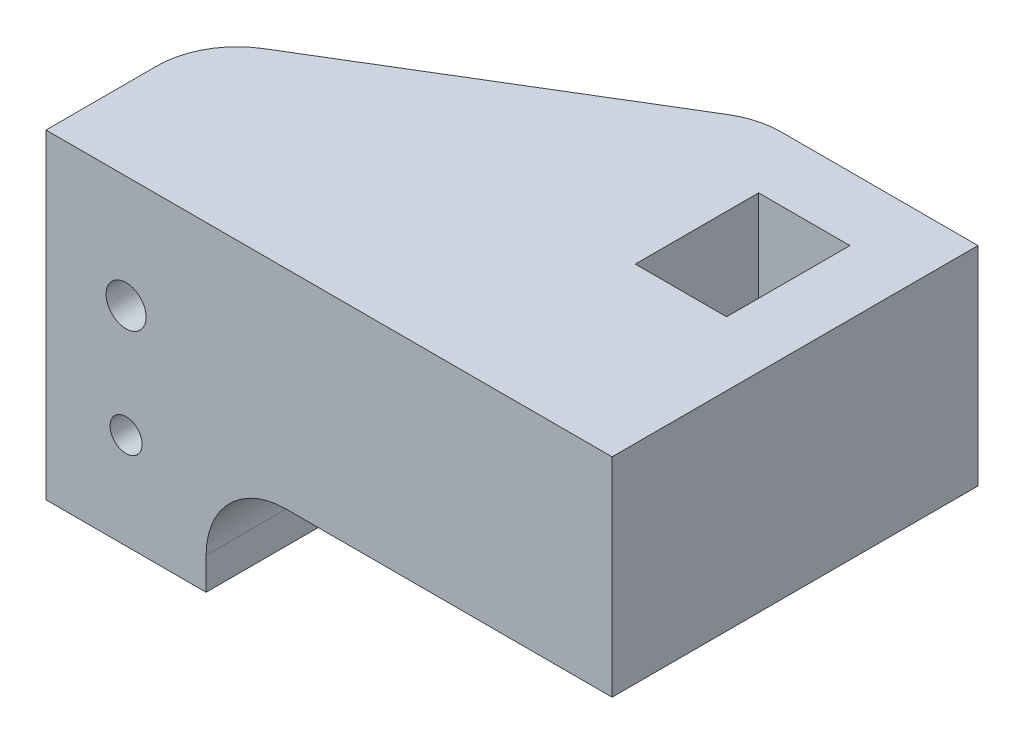
SolidWorks part; units mm, degrees
ref_plane "Plan de face" through (0, 0, 0) normal (0, 0, 1) x (1, 0, 0)
ref_plane "Plan de dessus" through (0, 0, 0) normal (0, 1, 0) x (1, 0, 0)
ref_plane "Plan de droite" through (0, 0, 0) normal (1, 0, 0) x (0, 0, -1)
sketch "Esquisse1" plane through (0, 0, 0) normal (0, 1, 0) x (1, 0, 0)
  line L0 (0, 0) -> (-56, 0) construction
  line L1 (0, 0) -> (0, 16.9732) construction
  line L2 (-32.5, 10) -> (0, 10) construction
  circle A0 centre (-56, 0) radius 3.5 construction
  circle A1 centre (56, 0) radius 3.5 construction
  circle A2 centre (-32.5, 10) radius 3.5 construction
  circle A3 centre (32.5, 10) radius 3.5 construction
  point P12 (0, 0)
  dimension "D1" = 7
  dimension "D3" = 7
  dimension "D2" = 112
  dimension "D4" = 65
  dimension "D5" = 10
sketch "Esquisse2" plane through (0, 0, 0) normal (0, 1, 0) x (1, 0, 0)
  line L0 (-35.35, 13.85) -> (-29.65, 6.15) construction
  line L1 (-35.35, 13.85) -> (-29.65, 13.85)
  line L2 (-35.35, 13.85) -> (-35.35, 6.15)
  line L3 (-35.35, 6.15) -> (-29.65, 6.15)
  line L4 (-29.65, 13.85) -> (-29.65, 6.15)
  line L5 (-29.65, 13.85) -> (-35.35, 6.15) construction
  line L6 (-61, -5) -> (-51.5843, -5)
  line L7 (-51.5843, -5) -> (-25.65, -5)
  line L8 (-25.65, -5) -> (-25.65, 17.85)
  line L9 (-25.65, 17.85) -> (-39.35, 17.85)
  line L10 (-39.35, 17.85) -> (-61, 4.7503)
  line L11 (-61, 4.7503) -> (-61, -5)
  point P4 (-24.318, 14.9899)
  point P5 (-32.5, 10)
  point P13 (-36.9704, 16.3434)
  dimension "D1" = 5.7
  dimension "D2" = 7.7
  dimension "D3" = 5
  dimension "D4" = 5
  dimension "D5" = 4
  dimension "D6" = 4
  dimension "D7" = 4
extrude "Boss.-Extru.1" add sketch "Esquisse2" along normal blind 20
sketch "Esquisse3" plane through (0, 0, 5) normal (0, 0, 1) x (1, 0, 0)
  line L0 (-56, 0) -> (-56, 20) construction
  line L1 (-52.5, 0) -> (-59.5, 0) construction
  line L2 (-61, 20) -> (-25.65, 20) construction
  line L3 (-56, 10) -> (-61, 10) construction
  line L4 (-61, 20) -> (-61, 0) construction
  line L5 (-25.65, 20) -> (-25.65, 0) construction
  line L6 (-51, 0) -> (-25.65, 0)
  line L7 (-51, 0) -> (-51, 7)
  line L8 (-51, 7) -> (-25.65, 7)
  line L9 (-25.65, 0) -> (-25.65, 7)
  circle A0 centre (-56, 12.9999) radius 1.25
  circle A1 centre (-56, 5.9999) radius 1
  dimension "D1" = 2
  dimension "D2" = 2.5
  dimension "D3" = 7
  dimension "D4" = 7
  dimension "D5" = 10
extrude "Enlèv. mat.-Extru.1" cut sketch "Esquisse3" against normal through all
fillet "Congé1" radius 5 1 edges at (-51, 7, -2.9005)
fillet "Congé2" radius 5 2 edges at (-39.35, 13.5, -17.85) (-61, 10, -4.7503)
